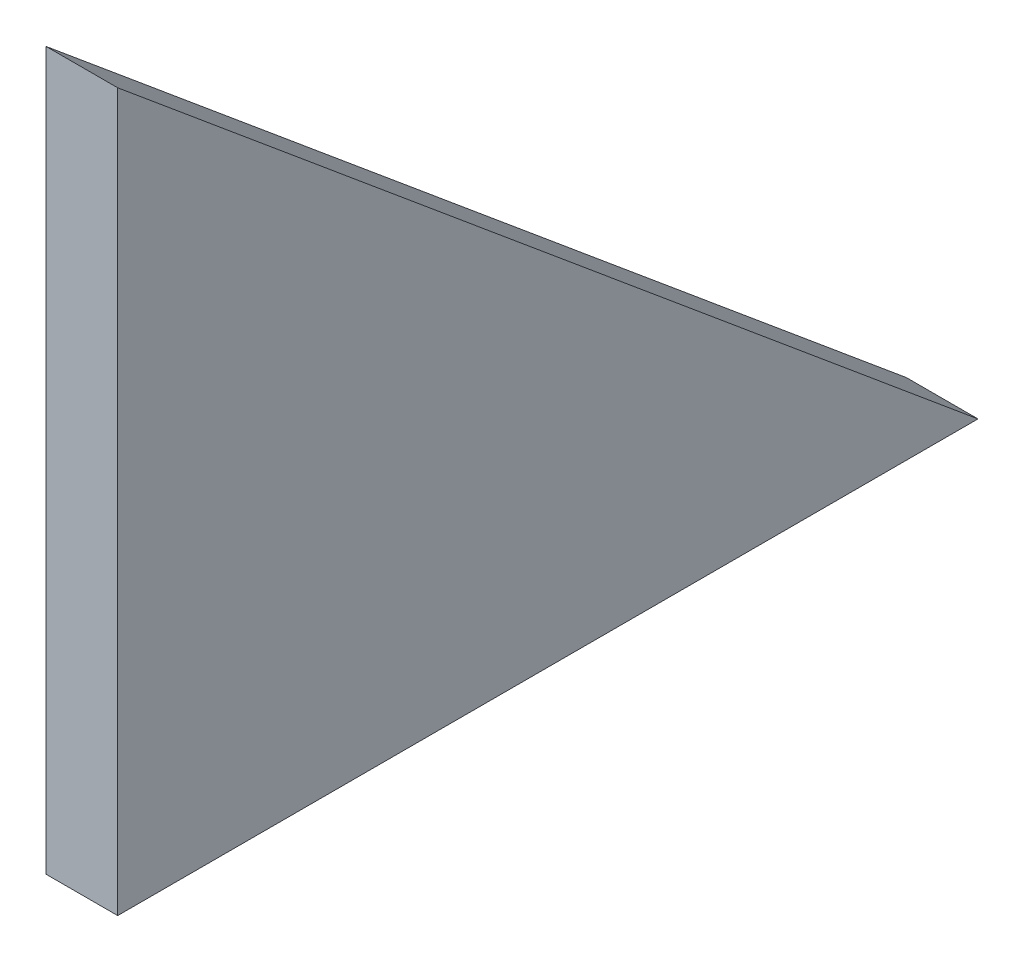
SolidWorks part; units mm, degrees
ref_plane "Спереди" through (0, 0, 0) normal (0, 0, 1) x (1, 0, 0)
ref_plane "Сверху" through (0, 0, 0) normal (0, 1, 0) x (1, 0, 0)
ref_plane "Справа" through (0, 0, 0) normal (1, 0, 0) x (0, 0, -1)
sketch "Эскиз1" plane through (0, 0, 0) normal (1, 0, 0) x (0, 0, -1)
  line L0 (0, 0) -> (60, 0)
  line L1 (60, 0) -> (0, 50)
  line L2 (0, 50) -> (0, 0)
extrude "Бобышка-Вытянуть1" add sketch "Эскиз1" along normal blind 5
